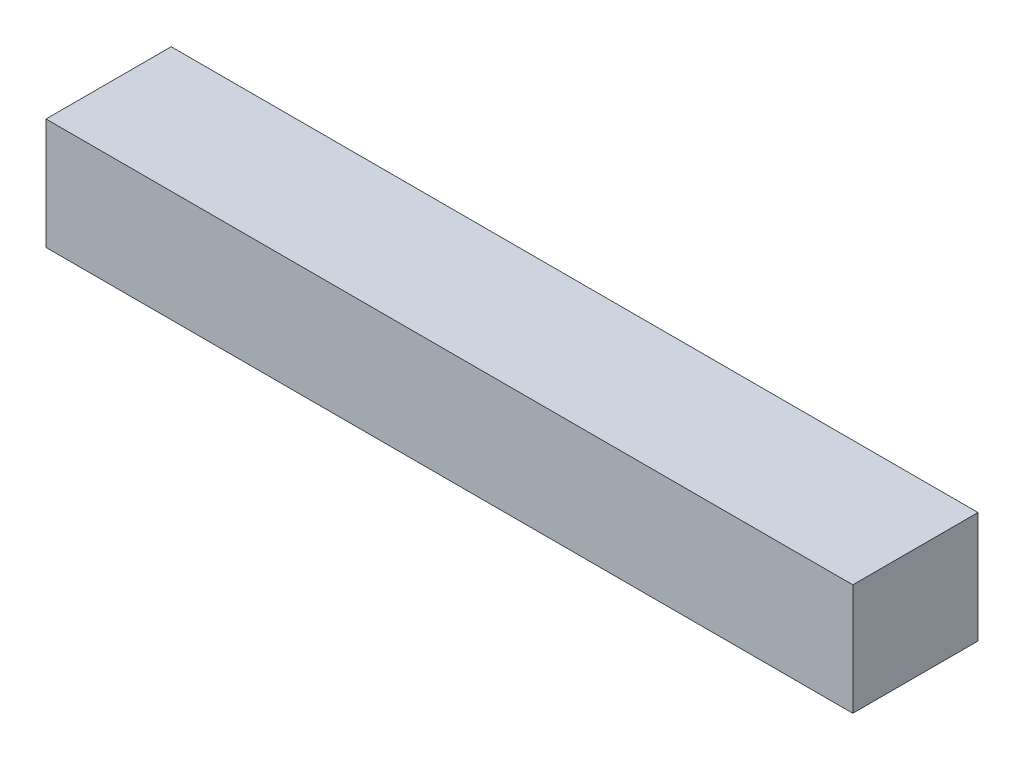
SolidWorks part; units mm, degrees
ref_plane "Front Plane" through (0, 0, 0) normal (0, 0, 1) x (1, 0, 0)
ref_plane "Top Plane" through (0, 0, 0) normal (0, 1, 0) x (1, 0, 0)
ref_plane "Right Plane" through (0, 0, 0) normal (1, 0, 0) x (0, 0, -1)
sketch "Sketch2" plane through (0, 0, 0) normal (0, 1, 0) x (1, 0, 0)
  line L1 (-29, 4.5) -> (29, 4.5)
  line L2 (-29, 4.5) -> (-29, -4.5)
  line L3 (-29, -4.5) -> (29, -4.5)
  line L4 (29, 4.5) -> (29, -4.5)
  line L5 (-29, 4.5) -> (29, -4.5) construction
  line L6 (-29, -4.5) -> (29, 4.5) construction
  point P0 (0, 0)
extrude "Boss-Extrude1" add sketch "Sketch2" along normal blind 8
